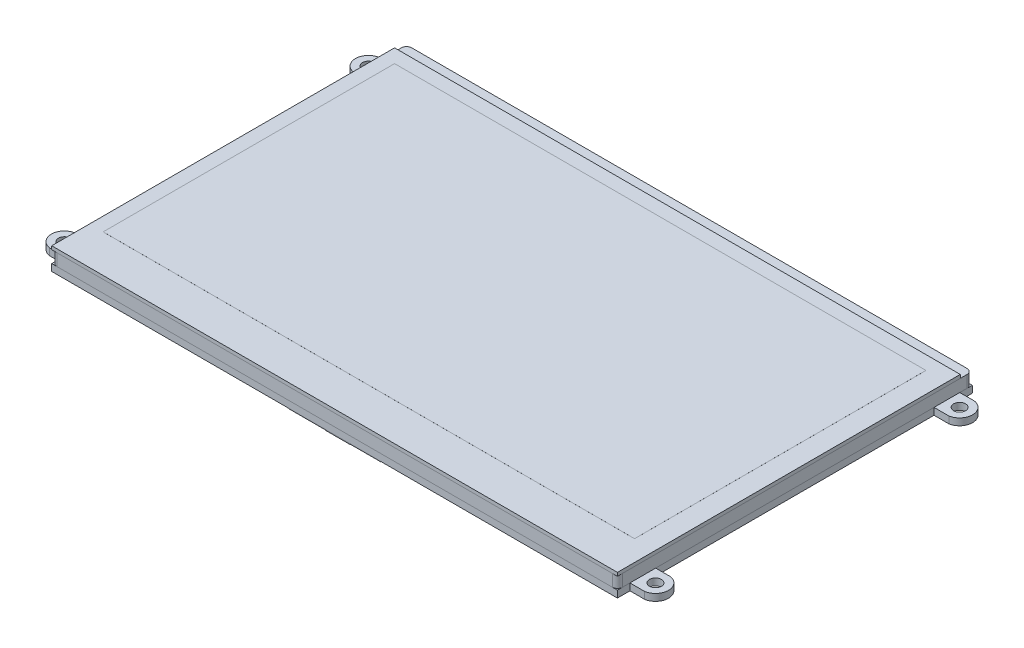
SolidWorks part; units mm, degrees
ref_plane "Plan de face" through (0, 0, 0) normal (0, 0, 1) x (1, 0, 0)
ref_plane "Plan de dessus" through (0, 0, 0) normal (0, 1, 0) x (1, 0, 0)
ref_plane "Plan de droite" through (0, 0, 0) normal (1, 0, 0) x (0, 0, -1)
sketch "Esquisse1" plane through (0, 0, 0) normal (0, 1, 0) x (1, 0, 0)
  line L1 (-82.5, 50) -> (82.5, 50)
  line L2 (-82.5, 50) -> (-82.5, -50)
  line L3 (-82.5, -50) -> (82.5, -50)
  line L4 (82.5, 50) -> (82.5, -50)
  line L5 (-82.5, 50) -> (82.5, -50) construction
  line L6 (-82.5, -50) -> (82.5, 50) construction
  point P0 (0, 0)
  dimension "D1" = 100
  dimension "D2" = 165
extrude "Boss.-Extru.1" add sketch "Esquisse1" along normal blind 1
sketch "Esquisse3" plane through (0, 0, 0) normal (0, -1, 0) x (1, 0, 0)
  line L2 (-82.5, 50) -> (82.5, 50)
  line L3 (-82.5, 50) -> (-82.5, -53.5)
  line L4 (-82.5, -53.5) -> (82.5, -53.5)
  line L5 (82.5, 50) -> (82.5, -53.5)
  line L6 (82.5, 50) -> (82.5, -50) construction
  line L9 (-82.5, 50) -> (82.5, 50) construction
  line L10 (-82.5, -50) -> (-82.5, 50) construction
  dimension "D1" = 103.5
extrude "Boss.-Extru.2" add sketch "Esquisse3" along normal blind 3.5 separate body
fillet "Congé1" radius 1.5 4 edges at (-82.5, -1.75, -53.5) (82.5, -1.75, -53.5) (82.5, -1.75, 50) (-82.5, -1.75, 50)
sketch "Esquisse4" plane through (0, -3.5, 0) normal (0, -1, 0) x (1, 0, 0)
  line L0 (-82.5, 48.5) -> (-82.5, -52) construction
  line L1 (82.5, -53.5) -> (-82.5, -53.5)
  line L2 (82.5, -53.5) -> (82.5, -49.85)
  line L3 (82.5, 50) -> (-82.5, 50)
  line L4 (-82.5, -53.5) -> (-82.5, -49.85)
  line L5 (81, 50) -> (-81, 50) construction
  line L6 (-81, -53.5) -> (81, -53.5) construction
  line L7 (82.5, -52) -> (82.5, 48.5) construction
  line L8 (0, 50) -> (0, -53.5) construction
  line L9 (82.5, 46.35) -> (86.8144, 46.35)
  line L10 (-82.5, 46.35) -> (-82.5, 50)
  line L11 (82.5, 38.85) -> (86.8144, 38.85)
  line L12 (-82.5, -1.75) -> (82.5, -1.75) construction
  line L13 (-82.5, 38.85) -> (-86.8144, 38.85)
  line L14 (-82.5, 46.35) -> (-86.8144, 46.35)
  line L15 (-82.5, -49.85) -> (-86.8144, -49.85)
  line L16 (-82.5, -42.35) -> (-86.8144, -42.35)
  line L17 (82.5, -42.35) -> (86.8144, -42.35)
  line L18 (82.5, -49.85) -> (86.8144, -49.85)
  line L19 (82.5, 46.35) -> (82.5, 50)
  line L20 (-82.5, -42.35) -> (-82.5, 38.85)
  line L21 (82.5, -42.35) -> (82.5, 38.85)
  arc A0 (86.8144, 38.85) -> (86.8144, 46.35) centre (86.2, 42.6) ccw
  circle A1 centre (86.2, 42.6) radius 1.75
  circle A2 centre (-86.2, 42.6) radius 1.75
  arc A3 (-86.8144, 38.85) -> (-86.8144, 46.35) centre (-86.2, 42.6) cw
  arc A4 (-86.8144, -42.35) -> (-86.8144, -49.85) centre (-86.2, -46.1) ccw
  circle A5 centre (-86.2, -46.1) radius 1.75
  circle A6 centre (86.2, -46.1) radius 1.75
  arc A7 (86.8144, -42.35) -> (86.8144, -49.85) centre (86.2, -46.1) cw
  dimension "D3" = 3.5
  dimension "D1" = 7.5
  dimension "D2" = 7.4
  dimension "D4" = 7.5
  dimension "D5" = 3.7
  dimension "D6" = 7.4
extrude "Boss.-Extru.3" add sketch "Esquisse4" along normal blind 2 separate body
other "Enregistrer les corps1"
sketch "Esquisse6" plane through (0, -5.5, 0) normal (0, -1, 0) x (1, 0, 0)
  line L0 (13.5, 50) -> (13.5, 21.5)
  line L1 (82.5, 50) -> (-82.5, 50) construction
  line L2 (13.5, 21.5) -> (-40.5, 21.5)
  line L3 (-40.5, 21.5) -> (-40.5, -14)
  line L4 (-40.5, -14) -> (-60.5, -14)
  line L5 (-60.5, -14) -> (-60.5, 45.5)
  line L6 (-60.5, 45.5) -> (-13.5, 45.5)
  line L7 (-13.5, 45.5) -> (-13.5, 50)
  line L8 (82.5, -42.35) -> (82.5, 38.85) construction
  line L9 (13.5, 50) -> (-13.5, 50)
  dimension "D1" = 28.5
  dimension "D2" = 54
  dimension "D3" = 20
  dimension "D4" = 47
  dimension "D5" = 64
  dimension "D6" = 24
  dimension "D7" = 69
extrude "Boss.-Extru.4" add sketch "Esquisse6" along normal blind 0.1 separate body
sketch "Esquisse7" plane through (0, -5.5, 0) normal (0, -1, 0) x (1, 0, 0)
  line L1 (-63, -14) -> (-38, -14)
  line L2 (-63, -14) -> (-63, -19.5)
  line L3 (-63, -19.5) -> (-38, -19.5)
  line L4 (-38, -14) -> (-38, -19.5)
  line L5 (-60.5, -14) -> (-40.5, -14) construction
  point P6 (-50.5, -14)
  point P7 (-50.5, -14)
  dimension "D1" = 25
  dimension "D2" = 5.5
extrude "Boss.-Extru.5" add sketch "Esquisse7" along normal blind 2
sketch "Esquisse9" plane through (0, -5.6, 0) normal (0, -1, 0) x (1, 0, 0)
  line L0 (13.5, 50) -> (-13.5, 50) construction
  line L1 (-2.5, 50) -> (4.5, 50)
  line L2 (-2.5, 50) -> (-2.5, -10)
  line L3 (-2.5, -10) -> (4.5, -10)
  line L4 (4.5, 50) -> (4.5, -10)
  line L5 (13.5, 21.5) -> (13.5, 50) construction
  dimension "D1" = 7
  dimension "D2" = 60
  dimension "D3" = 9
extrude "Boss.-Extru.6" add sketch "Esquisse9" along normal blind 0.1
sketch "Esquisse10" plane through (0, -5.5, 0) normal (0, -1, 0) x (1, 0, 0)
  line L0 (-2.5, -10) -> (4.5, -10) construction
  line L1 (-5.5, -10) -> (7.5, -10)
  line L2 (-5.5, -10) -> (-5.5, -15)
  line L3 (-5.5, -15) -> (7.5, -15)
  line L4 (7.5, -10) -> (7.5, -15)
  point P4 (1, -10)
  point P7 (1, -10)
  dimension "D1" = 5
  dimension "D2" = 13
extrude "Boss.-Extru.8" add sketch "Esquisse10" along normal blind 2
sketch "Esquisse11" plane through (0, 1, 0) normal (0, 1, 0) x (1, 0, 0)
  line L0 (82.5, -50) -> (82.5, 50) construction
  line L1 (-78.5, 46) -> (76.5, 46)
  line L2 (-78.5, 46) -> (-78.5, -39)
  line L3 (-78.5, -39) -> (76.5, -39)
  line L4 (76.5, 46) -> (76.5, -39)
  line L5 (-82.5, -50) -> (82.5, -50) construction
  line L8 (-1, 46) -> (-1, -39) construction
  line L9 (-78.5, 3.5) -> (76.5, 3.5) construction
  point P12 (-78.5, 3.5)
  point P13 (-1, 46)
  dimension "D1" = 85
  dimension "D2" = 155
  dimension "D3" = 6
  dimension "D4" = 11
extrude "Boss.-Extru.9" add sketch "Esquisse11" along normal blind 0.01
ref_plane "Plan1" through (0, 0, -3.5) normal (0, 0, 1) x (1, 0, 0)
